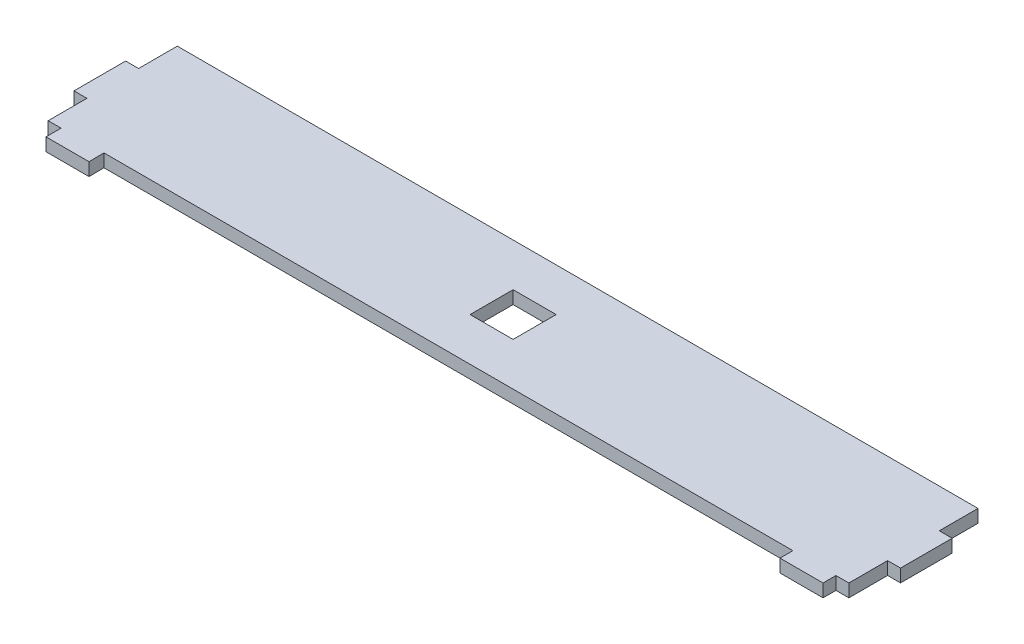
SolidWorks part; units mm, degrees
ref_plane "前视基准面" through (0, 0, 0) normal (0, 0, 1) x (1, 0, 0)
ref_plane "上视基准面" through (0, 0, 0) normal (0, 1, 0) x (1, 0, 0)
ref_plane "右视基准面" through (0, 0, 0) normal (1, 0, 0) x (0, 0, -1)
sketch "草图4" plane through (0, 0, 0) normal (0, 1, 0) x (1, 0, 0)
  line L0 (0, 0) -> (0.05, 0)
  line L1 (0, 0) -> (0.05, 0)
  line L3 (0, 30) -> (180, 30)
  line L5 (0, 0) -> (0, -3.5048)
  line L6 (0, 0) -> (0.05, 0)
  line L7 (10, 0) -> (9.95, 0)
  line L8 (0, -3.5048) -> (10, -3.5048)
  line L9 (10, -3.5048) -> (9.95, 0)
  line L10 (180, 0) -> (179.95, 0)
  line L11 (180, 0) -> (180, -3)
  line L12 (180, 0) -> (179.95, 0)
  line L13 (170, 0) -> (170.05, 0)
  line L14 (180, -3) -> (170, -3)
  line L15 (170, -3) -> (170, 0)
  line L24 (-3, 21) -> (-6, 21)
  line L25 (-6, 21) -> (-6, 9)
  line L26 (-6, 9) -> (-3, 9)
  line L27 (-3, 21) -> (-3, 30)
  line L28 (-3, 30) -> (0, 30)
  line L29 (-3, 9) -> (-3, 0)
  line L30 (-3, 0) -> (0, 0)
  line L31 (9.95, 0) -> (170.05, 0)
  line L32 (9.95, 0) -> (10, 0)
  line L33 (170.05, 0) -> (170, 0)
  line L34 (179.95, 0) -> (180, 0)
  line L35 (179.95, 0) -> (183, 0)
  line L36 (183, 0) -> (183, 9)
  line L37 (183, 21) -> (183, 30)
  line L38 (183, 30) -> (180, 30)
  line L39 (183, 21) -> (186, 21)
  line L40 (186, 21) -> (186, 9)
  line L41 (186, 9) -> (183, 9)
  line L43 (85, 10) -> (95, 10)
  line L44 (95, 10) -> (95, 20)
  line L45 (95, 20) -> (85, 20)
  line L46 (85, 20) -> (85, 10)
  point P32 (90, 10)
extrude "凸台-拉伸1" add sketch "草图4" along normal blind 3
